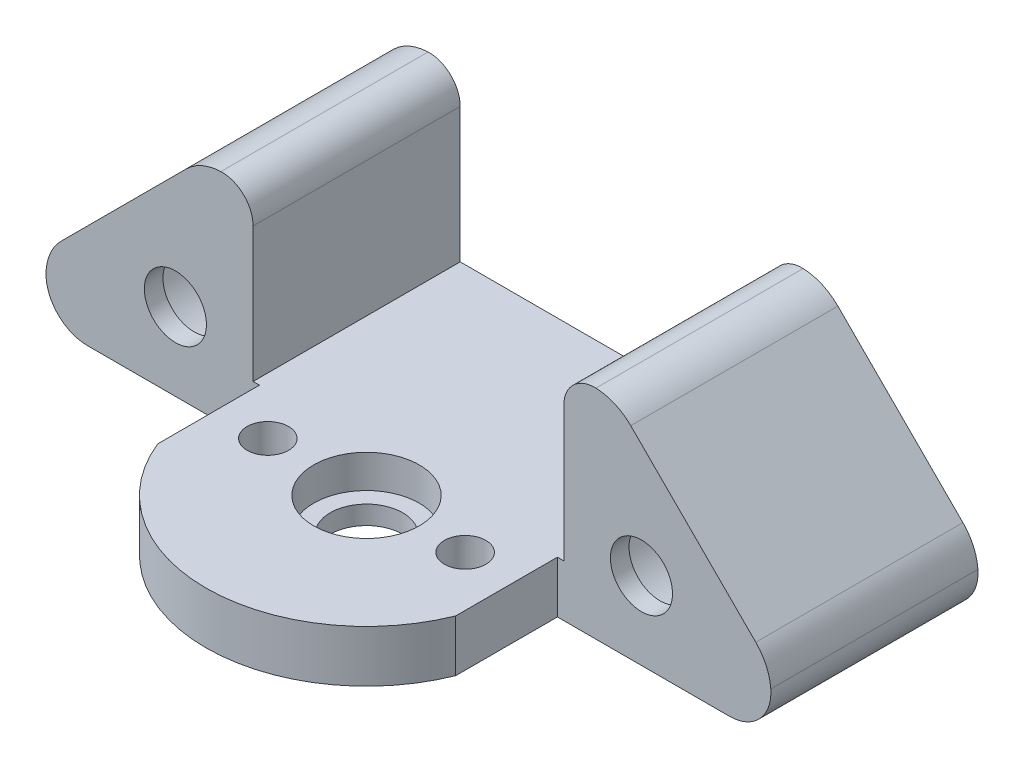
SolidWorks part; units mm, degrees
ref_plane "Plan de face" through (0, 0, 0) normal (0, 0, 1) x (1, 0, 0)
ref_plane "Plan de dessus" through (0, 0, 0) normal (0, 1, 0) x (1, 0, 0)
ref_plane "Plan de droite" through (0, 0, 0) normal (1, 0, 0) x (0, 0, -1)
sketch "Esquisse1" plane through (0, 0, 0) normal (0, 1, 0) x (1, 0, 0)
  line L1 (-14.385, -5.7725) -> (-14.385, 24.05)
  line L2 (14.385, -5.7725) -> (14.385, 24.05)
  line L3 (-14.385, 24.05) -> (14.385, 24.05)
  line L4 (-14.385, -5.7725) -> (14.385, -5.7725) construction
  line L5 (0, 0) -> (-14.385, 0) construction
  line L6 (0, 0) -> (0, -15.5) construction
  circle A0 centre (0, 0) radius 15.5 construction
  arc A1 (-14.385, -5.7725) -> (14.385, -5.7725) centre (0, 0) ccw
  circle A2 centre (0, 0) radius 3.5
  dimension "D1" = 31
  dimension "D3" = 7
  dimension "D2" = 28.77
  dimension "D4" = 24.05
extrude "Boss.-Extru.1" add sketch "Esquisse1" along normal blind 5
sketch "Esquisse2" plane through (0, 5, 0) normal (0, 1, 0) x (1, 0, 0)
  circle A0 centre (0, 0) radius 5.1
  dimension "D1" = 10.2
extrude "Enlèv. mat.-Extru.1" cut sketch "Esquisse2" against normal blind 3.2
sketch "Esquisse3" plane through (0, 5, 0) normal (0, 1, 0) x (1, 0, 0)
  line L0 (9.525, 0) -> (-9.525, 0) construction
  circle A0 centre (-9.525, 0) radius 2
  circle A1 centre (9.525, 0) radius 2
  point P8 (0, 0)
  dimension "D1" = 4
  dimension "D2" = 19.05
extrude "Enlèv. mat.-Extru.2" cut sketch "Esquisse3" against normal blind 5
sketch "Esquisse4" plane through (0, 0, -24.05) normal (0, 0, -1) x (-1, 0, 0)
  line L0 (30, 0) -> (15, 15) construction
  line L1 (15, 0) -> (30, 0) construction
  line L3 (15, 15) -> (30, 15) construction
  line L4 (30, 0) -> (30, 15) construction
  line L5 (-15, 0) -> (-30, 0) construction
  line L6 (-15, 0) -> (-15, 15) construction
  line L7 (-15, 15) -> (-30, 15) construction
  line L8 (-30, 0) -> (-30, 15) construction
  line L9 (-15, 15) -> (-30, 0) construction
  line L10 (-15, 0) -> (15, 0) construction
  line L12 (-14.385, 0) -> (-15, 0) construction
  line L13 (-14.385, 0) -> (-14.385, 5)
  line L14 (-14.385, 5) -> (-15, 5)
  line L15 (-15, 0) -> (-15, 5) construction
  line L17 (14.385, 0) -> (14.385, 5)
  line L18 (14.385, 5) -> (15, 5)
  line L19 (15, 0) -> (15, 5) construction
  line L20 (15, 15) -> (15, 5) construction
  line L21 (15, 5) -> (15, 21)
  line L24 (-14.385, 0) -> (-35, 0)
  line L25 (-15, 21) -> (-15, 5)
  line L26 (15, 21) -> (20, 21)
  line L27 (20, 21) -> (35, 6)
  line L28 (35, 6) -> (35, 0)
  line L29 (14.385, 0) -> (35, 0)
  line L30 (-35, 0) -> (-35, 6)
  line L31 (-35, 6) -> (-20, 21)
  line L32 (-20, 21) -> (-15, 21)
  circle A0 centre (22.5, 7.5) radius 3
  circle A1 centre (-22.5, 7.5) radius 3
  circle A2 centre (22.5, 7.5) radius 7.5 construction
  point P18 (0, 0)
  dimension "D3" = 6
  dimension "D5" = 6
  dimension "D1" = 15
  dimension "D2" = 16
  dimension "D4" = 30
  dimension "D6" = 20
  dimension "D7" = 5
extrude "Boss.-Extru.2" add sketch "Esquisse4" against normal blind 20
sketch "Esquisse5" plane through (0, 0, -24.05) normal (0, 0, -1) x (-1, 0, 0)
  circle A0 centre (22.5, 7.5) radius 6.1
  circle A1 centre (-22.5, 7.5) radius 6.1
  dimension "D1" = 12.2
extrude "Enlèv. mat.-Extru.3" cut sketch "Esquisse5" against normal offset from surface (18.2 mm away) 1.8 up to face at (-25.5, 7.5, -4.05)
sketch "Esquisse6" plane through (0, 0, 0) normal (0, -1, 0) x (1, 0, 0)
  line L0 (8.3424, -19.359) -> (8.3435, -18.3296)
  line L1 (8.3431, -15.8309) -> (8.3393, -12.3102)
  line L2 (8.3393, -12.3102) -> (8.3096, -12.2236)
  line L3 (7.7525, -11.6731) -> (7.6592, -11.6435)
  line L4 (7.6592, -11.6435) -> (4.111, -11.6435)
  line L5 (4.111, -11.6435) -> (0.5629, -11.6435)
  line L6 (0.5629, -11.6435) -> (0.5151, -11.6799)
  line L7 (0.5315, -13.6871) -> (0.5756, -13.7171)
  line L8 (0.5756, -13.7171) -> (3.3311, -13.7171)
  line L9 (3.3311, -13.7171) -> (6.0867, -13.7171)
  line L10 (6.0867, -13.7171) -> (6.1462, -13.7471)
  line L11 (6.2357, -13.8366) -> (6.2657, -13.8961)
  line L12 (6.2657, -13.8961) -> (6.2657, -16.6516)
  line L13 (6.2657, -16.6516) -> (6.2657, -19.4072)
  line L14 (6.2657, -19.4072) -> (6.2957, -19.4513)
  line L15 (-0.492, -11.6799) -> (-0.5398, -11.6435)
  line L16 (-0.5398, -11.6435) -> (-1.4209, -11.6398)
  line L17 (-2.4453, -11.7212) -> (-2.4754, -11.7635)
  line L18 (-2.4754, -11.7635) -> (-2.4821, -13.0837)
  line L19 (-2.4821, -13.0837) -> (-2.4888, -14.4038)
  line L20 (-2.4888, -14.4038) -> (-2.5193, -14.4529)
  line L21 (-4.3842, -14.554) -> (-6.1025, -14.5505)
  line L22 (-6.1025, -14.5505) -> (-6.1474, -14.5185)
  line L23 (-6.2423, -13.0825) -> (-6.2426, -11.7875)
  line L24 (-6.2426, -11.7875) -> (-6.2726, -11.7434)
  line L25 (-8.2887, -11.7353) -> (-8.3162, -11.7721)
  line L26 (-8.3162, -11.7721) -> (-8.3162, -15.3216)
  line L27 (-8.3162, -15.3216) -> (-8.3162, -18.8711)
  line L28 (-8.3162, -18.8711) -> (-8.2866, -18.9644)
  line L29 (-7.7361, -19.5215) -> (-7.6494, -19.5511)
  line L30 (-7.6494, -19.5511) -> (-4.3957, -19.5535)
  line L31 (-6.1474, -16.6761) -> (-6.1025, -16.6441)
  line L32 (-6.1025, -16.6441) -> (-4.3835, -16.6406)
  line L33 (-4.3636, -17.4775) -> (-6.0636, -17.4776)
  line L34 (-6.0636, -17.4776) -> (-6.1231, -17.4476)
  line L35 (0, 0) -> (0, -24.05) construction
  line L36 (35, -24.05) -> (-35, -24.05) construction
  arc A0 (8.2199, -19.5392) -> (8.2591, -19.515) centre (8.1532, -19.3873) ccw
  arc A1 (8.2591, -19.515) -> (8.2961, -19.4778) centre (8.0827, -19.3024) ccw
  arc A2 (8.2961, -19.4778) -> (8.3249, -19.435) centre (8.0888, -19.3073) ccw
  arc A3 (8.3249, -19.435) -> (8.3392, -19.3941) centre (8.2045, -19.3699) ccw
  arc A4 (8.3392, -19.3941) -> (8.3424, -19.359) centre (8.1421, -19.3587) ccw
  arc A5 (8.3435, -18.3296) -> (8.344, -17.1835) centre (-841.8612, -17.408) ccw
  arc A6 (8.344, -17.1835) -> (8.3431, -15.8309) centre (-1633.4644, -17.6174) ccw
  arc A7 (8.3096, -12.2236) -> (8.2219, -12.0399) centre (7.4762, -12.5086) ccw
  arc A8 (8.2219, -12.0399) -> (8.0943, -11.8808) centre (7.47, -12.5126) ccw
  arc A9 (8.0943, -11.8808) -> (7.9346, -11.756) centre (7.478, -12.5045) ccw
  arc A10 (7.9346, -11.756) -> (7.7525, -11.6731) centre (7.5011, -12.4666) ccw
  arc A11 (0.5151, -11.6799) -> (0.4603, -11.7503) centre (0.6214, -11.8192) ccw
  arc A12 (0.4603, -11.7503) -> (0.4348, -11.8525) centre (0.7645, -11.8805) ccw
  arc A13 (0.4348, -11.8525) -> (0.4264, -12.0509) centre (2.763, -12.0505) ccw
  arc A14 (0.4264, -12.0509) -> (0.4278, -12.706) centre (156.8589, -12.0298) ccw
  arc A15 (0.4278, -12.706) -> (0.4308, -13.2803) centre (327.5128, -11.2927) ccw
  arc A16 (0.4308, -13.2803) -> (0.4347, -13.4731) centre (7.1728, -13.2394) ccw
  arc A17 (0.4347, -13.4731) -> (0.4419, -13.5745) centre (1.8331, -13.4246) ccw
  arc A18 (0.4419, -13.5745) -> (0.4595, -13.6194) centre (0.5334, -13.5647) ccw
  arc A19 (0.4595, -13.6194) -> (0.4733, -13.636) centre (0.6093, -13.5084) ccw
  arc A20 (0.4733, -13.636) -> (0.4921, -13.6548) centre (0.7828, -13.3456) ccw
  arc A21 (0.4921, -13.6548) -> (0.5126, -13.6729) centre (0.7917, -13.3361) ccw
  arc A22 (0.5126, -13.6729) -> (0.5315, -13.6871) centre (0.6724, -13.48) ccw
  arc A23 (6.1757, -13.7645) -> (6.1462, -13.7471) centre (6.0275, -13.9823) ccw
  arc A24 (6.199, -13.7838) -> (6.1757, -13.7645) centre (6.0851, -13.8976) ccw
  arc A25 (6.2183, -13.8071) -> (6.199, -13.7838) centre (6.0851, -13.8976) ccw
  arc A26 (6.2357, -13.8366) -> (6.2183, -13.8071) centre (6.0004, -13.9552) ccw
  arc A27 (6.2957, -19.4513) -> (6.3099, -19.4702) centre (6.5028, -19.3103) ccw
  arc A28 (6.3099, -19.4702) -> (6.3279, -19.4906) centre (6.6467, -19.191) ccw
  arc A29 (6.3279, -19.4906) -> (6.3467, -19.5094) centre (6.6371, -19.2) ccw
  arc A30 (6.3467, -19.5094) -> (6.3633, -19.5233) centre (6.4743, -19.3735) ccw
  arc A31 (6.3633, -19.5233) -> (6.4084, -19.5408) centre (6.418, -19.4494) ccw
  arc A32 (6.4084, -19.5408) -> (6.511, -19.5479) centre (6.5588, -18.1145) ccw
  arc A33 (6.511, -19.5479) -> (6.7061, -19.5517) centre (6.741, -12.6408) ccw
  arc A34 (6.7061, -19.5517) -> (7.2901, -19.5541) centre (8.4226, 320.7484) ccw
  arc A35 (7.2901, -19.5541) -> (7.7584, -19.555) centre (7.8083, 136.1356) ccw
  arc A36 (7.7584, -19.555) -> (8.0122, -19.553) centre (7.7634, -4.0244) ccw
  arc A37 (8.0122, -19.553) -> (8.1762, -19.5491) centre (7.8401, -8.8093) ccw
  arc A38 (8.1762, -19.5491) -> (8.2199, -19.5392) centre (8.1726, -19.4314) ccw
  arc A39 (-1.0592, -19.5378) -> (-0.9323, -19.4971) centre (-1.2082, -18.8551) ccw
  arc A40 (-0.9323, -19.4971) -> (-0.8057, -19.4307) centre (-1.298, -18.6462) ccw
  arc A41 (-0.8057, -19.4307) -> (-0.6892, -19.3445) centre (-1.3107, -18.6259) ccw
  arc A42 (-0.6892, -19.3445) -> (-0.5924, -19.245) centre (-1.2133, -18.7385) ccw
  arc A43 (-0.5924, -19.245) -> (-0.5471, -19.1825) centre (-1.1187, -18.8157) ccw
  arc A44 (-0.5471, -19.1825) -> (-0.5039, -19.1085) centre (-1.4116, -18.6277) ccw
  arc A45 (-0.5039, -19.1085) -> (-0.4652, -19.0277) centre (-1.491, -18.5856) ccw
  arc A46 (-0.4652, -19.0277) -> (-0.4332, -18.9444) centre (-1.47, -18.5947) ccw
  arc A47 (-0.4332, -18.9444) -> (-0.4167, -18.8484) centre (-0.7323, -18.8435) ccw
  arc A48 (-0.4167, -18.8484) -> (-0.4114, -18.3916) centre (-62.4377, -17.901) ccw
  arc A49 (-0.4114, -18.3916) -> (-0.4077, -17.5915) centre (-125.1963, -17.4045) ccw
  arc A50 (-0.4077, -17.5915) -> (-0.4048, -15.3506) centre (-4958.0599, -10.1594) ccw
  arc A51 (-0.4048, -15.3506) -> (-0.4028, -12.6642) centre (-4418.8192, -10.7214) ccw
  arc A52 (-0.4028, -12.6642) -> (-0.4097, -12.0726) centre (-24.8688, -12.6535) ccw
  arc A53 (-0.4097, -12.0726) -> (-0.43, -11.7885) centre (-3.4059, -12.1438) ccw
  arc A54 (-0.43, -11.7885) -> (-0.492, -11.6799) centre (-0.5893, -11.8075) ccw
  arc A55 (-1.4209, -11.6398) -> (-2.0735, -11.6383) centre (-2.0892, -169.2706) ccw
  arc A56 (-2.0735, -11.6383) -> (-2.2764, -11.6464) centre (-2.0738, -14.1947) ccw
  arc A57 (-2.2764, -11.6464) -> (-2.3796, -11.6701) centre (-2.2476, -12.0082) ccw
  arc A58 (-2.3796, -11.6701) -> (-2.4453, -11.7212) centre (-2.3267, -11.8058) ccw
  arc A59 (-2.5355, -14.4745) -> (-2.5193, -14.4529) centre (-2.6506, -14.3713) ccw
  arc A60 (-2.5573, -14.496) -> (-2.5355, -14.4745) centre (-2.7239, -14.3055) ccw
  arc A61 (-2.582, -14.5152) -> (-2.5573, -14.496) centre (-2.7302, -14.2983) ccw
  arc A62 (-2.6071, -14.5297) -> (-2.582, -14.5152) centre (-2.6924, -14.3535) ccw
  arc A63 (-2.6782, -14.5478) -> (-2.6071, -14.5297) centre (-2.6866, -14.3655) ccw
  arc A64 (-2.8726, -14.5536) -> (-2.6782, -14.5478) centre (-2.9544, -8.572) ccw
  arc A65 (-3.2386, -14.5559) -> (-2.8726, -14.5536) centre (-3.2089, 10.0519) ccw
  arc A66 (-4.3842, -14.554) -> (-3.2386, -14.5559) centre (-1.5552, 1381.7329) ccw
  arc A67 (-6.1664, -14.5023) -> (-6.1474, -14.5185) centre (-6.0638, -14.4012) ccw
  arc A68 (-6.1864, -14.4798) -> (-6.1664, -14.5023) centre (-5.9527, -14.2918) ccw
  arc A69 (-6.2044, -14.4551) -> (-6.1864, -14.4798) centre (-5.9473, -14.2875) ccw
  arc A70 (-6.2172, -14.4318) -> (-6.2044, -14.4551) centre (-6.0574, -14.3593) ccw
  arc A71 (-6.2326, -14.3682) -> (-6.2172, -14.4318) centre (-6.0574, -14.3593) ccw
  arc A72 (-6.2385, -14.2003) -> (-6.2326, -14.3682) centre (-1.0509, -14.1037) ccw
  arc A73 (-6.2415, -13.8959) -> (-6.2385, -14.2003) centre (11.6021, -13.8682) ccw
  arc A74 (-6.2423, -13.0825) -> (-6.2415, -13.8959) centre (606.4298, -12.944) ccw
  arc A75 (-6.2726, -11.7434) -> (-6.2868, -11.7245) centre (-6.4796, -11.8843) ccw
  arc A76 (-6.2868, -11.7245) -> (-6.3048, -11.704) centre (-6.6235, -12.0035) ccw
  arc A77 (-6.3048, -11.704) -> (-6.3236, -11.6852) centre (-6.614, -11.9946) ccw
  arc A78 (-6.3236, -11.6852) -> (-6.3402, -11.6714) centre (-6.4512, -11.8211) ccw
  arc A79 (-6.3402, -11.6714) -> (-6.3855, -11.6538) centre (-6.3948, -11.745) ccw
  arc A80 (-6.3855, -11.6538) -> (-6.489, -11.6471) centre (-6.5319, -13.0947) ccw
  arc A81 (-6.489, -11.6471) -> (-6.6862, -11.644) centre (-6.6979, -18.7037) ccw
  arc A82 (-6.6862, -11.644) -> (-7.2827, -11.6435) centre (-7.2823, -370.9961) ccw
  arc A83 (-7.2827, -11.6435) -> (-7.8759, -11.644) centre (-7.2825, -363.8852) ccw
  arc A84 (-7.8759, -11.644) -> (-8.0748, -11.6471) centre (-7.8637, -18.8776) ccw
  arc A85 (-8.0748, -11.6471) -> (-8.1797, -11.6537) centre (-8.0297, -13.1908) ccw
  arc A86 (-8.1797, -11.6537) -> (-8.2243, -11.671) centre (-8.171, -11.7424) ccw
  arc A87 (-8.2243, -11.671) -> (-8.2404, -11.6842) centre (-8.0864, -11.8557) ccw
  arc A88 (-8.2404, -11.6842) -> (-8.2584, -11.7012) centre (-7.9326, -12.027) ccw
  arc A89 (-8.2584, -11.7012) -> (-8.2755, -11.7192) centre (-7.9326, -12.027) ccw
  arc A90 (-8.2755, -11.7192) -> (-8.2887, -11.7353) centre (-8.1039, -11.8732) ccw
  arc A91 (-8.2866, -18.9644) -> (-8.2036, -19.1469) centre (-7.4865, -18.7109) ccw
  arc A92 (-8.2036, -19.1469) -> (-8.0791, -19.3064) centre (-7.4604, -18.695) ccw
  arc A93 (-8.0791, -19.3064) -> (-7.9202, -19.4337) centre (-7.4523, -18.6871) ccw
  arc A94 (-7.9202, -19.4337) -> (-7.7361, -19.5215) centre (-7.4486, -18.6812) ccw
  arc A95 (-4.3957, -19.5535) -> (-2.6408, -19.5541) centre (-2.7004, 2326.4659) ccw
  arc A96 (-2.6408, -19.5541) -> (-1.7427, -19.552) centre (-2.6458, 172.1945) ccw
  arc A97 (-1.7427, -19.552) -> (-1.1541, -19.5484) centre (-2.7343, 190.9613) ccw
  arc A98 (-1.1541, -19.5484) -> (-1.0592, -19.5378) centre (-1.1576, -19.087) ccw
  arc A99 (-6.1526, -17.4302) -> (-6.1231, -17.4476) centre (-6.0044, -17.2123) ccw
  arc A100 (-6.1759, -17.4109) -> (-6.1526, -17.4302) centre (-6.062, -17.297) ccw
  arc A101 (-6.1952, -17.3876) -> (-6.1759, -17.4109) centre (-6.062, -17.297) ccw
  arc A102 (-6.2126, -17.358) -> (-6.1952, -17.3876) centre (-5.9773, -17.2394) ccw
  arc A103 (-6.2293, -17.3156) -> (-6.2126, -17.358) centre (-5.9888, -17.2452) ccw
  arc A104 (-6.238, -17.271) -> (-6.2293, -17.3156) centre (-5.9947, -17.247) ccw
  arc A105 (-6.2416, -17.2036) -> (-6.238, -17.271) centre (-5.4799, -17.196) ccw
  arc A106 (-6.2423, -17.058) -> (-6.2416, -17.2036) centre (6.7029, -17.0738) ccw
  arc A107 (-6.2388, -16.8812) -> (-6.2423, -17.058) centre (-1.4966, -17.0638) ccw
  arc A108 (-6.2254, -16.7869) -> (-6.2388, -16.8812) centre (-5.7735, -16.8991) ccw
  arc A109 (-6.1972, -16.7259) -> (-6.2254, -16.7869) centre (-6.0516, -16.83) ccw
  arc A110 (-6.1474, -16.6761) -> (-6.1972, -16.7259) centre (-6.0232, -16.8504) ccw
  arc A111 (-3.2386, -16.6388) -> (-4.3835, -16.6406) centre (-1.5552, -1412.9275) ccw
  arc A112 (-2.8726, -16.6411) -> (-3.2386, -16.6388) centre (-3.2089, -41.2466) ccw
  arc A113 (-2.6782, -16.6469) -> (-2.8726, -16.6411) centre (-2.9544, -22.6227) ccw
  arc A114 (-2.6071, -16.6649) -> (-2.6782, -16.6469) centre (-2.6866, -16.8291) ccw
  arc A115 (-2.582, -16.6795) -> (-2.6071, -16.6649) centre (-2.6924, -16.8411) ccw
  arc A116 (-2.5573, -16.6986) -> (-2.582, -16.6795) centre (-2.7302, -16.8964) ccw
  arc A117 (-2.5355, -16.7201) -> (-2.5573, -16.6986) centre (-2.7239, -16.8892) ccw
  arc A118 (-2.5193, -16.7417) -> (-2.5355, -16.7201) centre (-2.6506, -16.8234) ccw
  arc A119 (-2.5019, -16.7793) -> (-2.5193, -16.7417) centre (-2.6634, -16.8314) ccw
  arc A120 (-2.4931, -16.8217) -> (-2.5019, -16.7793) centre (-2.6934, -16.841) ccw
  arc A121 (-2.4895, -16.8906) -> (-2.4931, -16.8217) centre (-3.2757, -16.8973) ccw
  arc A122 (-2.4888, -17.0575) -> (-2.4895, -16.8906) centre (-22.0267, -17.0575) ccw
  arc A123 (-2.4895, -17.2241) -> (-2.4888, -17.0575) centre (-21.915, -17.0575) ccw
  arc A124 (-2.4931, -17.2931) -> (-2.4895, -17.2241) centre (-3.2819, -17.2173) ccw
  arc A125 (-2.5018, -17.3356) -> (-2.4931, -17.2931) centre (-2.6952, -17.2737) ccw
  arc A126 (-2.5191, -17.373) -> (-2.5018, -17.3356) centre (-2.6613, -17.2846) ccw
  arc A127 (-2.535, -17.3941) -> (-2.5191, -17.373) centre (-2.6457, -17.2942) ccw
  arc A128 (-2.5569, -17.4158) -> (-2.535, -17.3941) centre (-2.7379, -17.2111) ccw
  arc A129 (-2.5815, -17.4352) -> (-2.5569, -17.4158) centre (-2.7433, -17.205) ccw
  arc A130 (-2.6058, -17.4496) -> (-2.5815, -17.4352) centre (-2.6877, -17.2841) ccw
  arc A131 (-2.6758, -17.4678) -> (-2.6058, -17.4496) centre (-2.6844, -17.2908) ccw
  arc A132 (-2.8684, -17.474) -> (-2.6758, -17.4678) centre (-2.9619, -11.5848) ccw
  arc A133 (-3.2308, -17.4771) -> (-2.8684, -17.474) centre (-3.251, 6.6213) ccw
  arc A134 (-4.3636, -17.4775) -> (-3.2308, -17.4771) centre (-4.372, 1343.1191) ccw
extrude "Enlèv. mat.-Extru.4" cut sketch "Esquisse6" against normal blind 1
fillet "Congé1" radius 5 4 edges at (-35, 6, -14.05) (-20, 21, -14.05) (20, 21, -14.05) (35, 6, -14.05)
fillet "Congé2" radius 3 2 edges at (-15, 21, -14.05) (15, 21, -14.05)
fillet "Congé3" radius 4 2 edges at (-35, 0, -14.05) (35, 0, -14.05)
